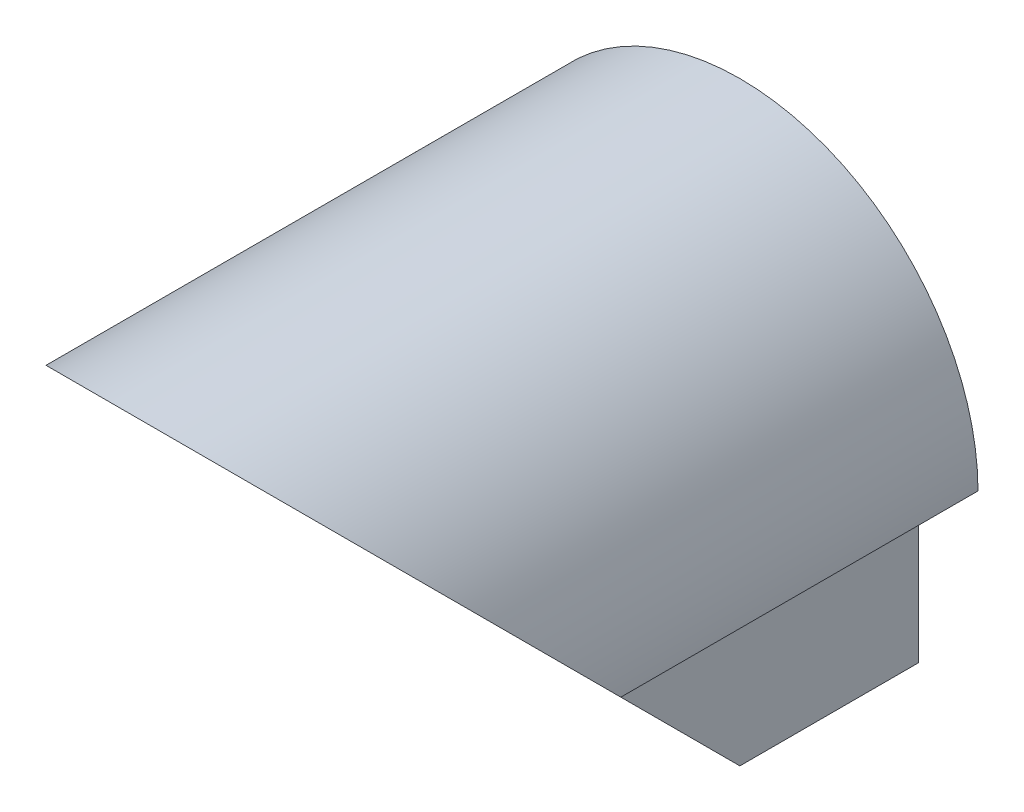
SolidWorks part; units mm, degrees
ref_plane "Front Plane" through (0, 0, 0) normal (0, 0, 1) x (1, 0, 0)
ref_plane "Top Plane" through (0, 0, 0) normal (0, 1, 0) x (1, 0, 0)
ref_plane "Right Plane" through (0, 0, 0) normal (1, 0, 0) x (0, 0, -1)
sketch "Sketch2" plane through (0, 0, 0) normal (0, 0, 1) x (1, 0, 0)
  line L0 (-4, -1) -> (-3, -1)
  line L1 (-2, -1) -> (2, -1)
  line L2 (-2, -1) -> (-2, 1)
  line L3 (-2, 1) -> (2, 1)
  line L4 (2, -1) -> (2, 1)
  line L5 (-2, -1) -> (2, 1) construction
  line L6 (-2, 1) -> (2, -1) construction
  line L7 (-3, -1) -> (-3, -4)
  line L8 (-3, -4) -> (-2, -4)
  line L9 (-2, -4) -> (-2, -3)
  line L10 (-2, -3) -> (-1, -3)
  line L11 (-1, -3) -> (-1, -2)
  line L12 (-1, -2) -> (1, -2)
  line L13 (1, -2) -> (1, -3)
  line L14 (1, -3) -> (2, -3)
  line L15 (2, -3) -> (2, -4)
  line L16 (2, -4) -> (3, -4)
  line L17 (3, -4) -> (3, -1)
  line L18 (3, -1) -> (4, -1)
  arc A0 (-4, -1) -> (4, -1) centre (0, -1) cw
  point P0 (0, 0)
  dimension "D1" = 4
  dimension "D2" = 2
  dimension "D3" = 3
  dimension "D4" = 3
  dimension "D5" = 1
  dimension "D6" = 1
  dimension "D7" = 1
  dimension "D8" = 1
  dimension "D9" = 1
  dimension "D10" = 2
  dimension "D11" = 1
  dimension "D12" = 1
  dimension "D13" = 1
  dimension "D14" = 1
  dimension "D15" = 1
  dimension "D16" = 1
  dimension "D17" = 1
extrude "Boss-Extrude1" add sketch "Sketch2" along normal mid plane 10
sketch "Sketch3" plane through (0, 0, 0) normal (1, 0, 0) x (0, 0, -1)
  line L0 (-5, 3) -> (2, -4)
  line L1 (-5, -4) -> (5, -4) construction
  line L2 (2, -4) -> (-5, -4)
  line L3 (-5, -4) -> (-5, 3)
  dimension "D1" = 3
extrude "Cut-Extrude1" cut sketch "Sketch3" against normal mid plane 8
